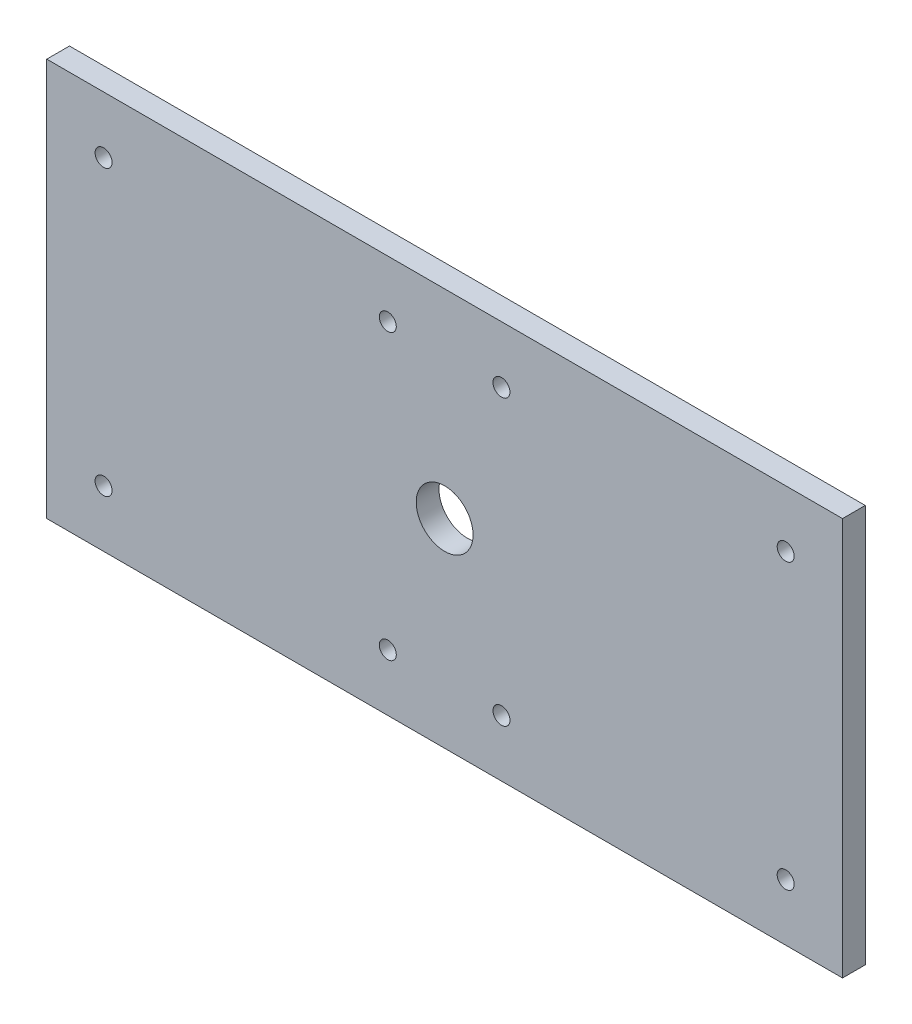
SolidWorks part; units mm, degrees
ref_plane "Front Plane" through (0, 0, 0) normal (0, 0, 1) x (1, 0, 0)
ref_plane "Top Plane" through (0, 0, 0) normal (0, 1, 0) x (1, 0, 0)
ref_plane "Right Plane" through (0, 0, 0) normal (1, 0, 0) x (0, 0, -1)
sketch "Sketch1" plane through (0, 0, 0) normal (0, 0, 1) x (1, 0, 0)
  line L1 (-88.9, 44.45) -> (88.9, 44.45)
  line L2 (-88.9, 44.45) -> (-88.9, -44.45)
  line L3 (-88.9, -44.45) -> (88.9, -44.45)
  line L4 (88.9, 44.45) -> (88.9, -44.45)
  line L5 (-88.9, 44.45) -> (88.9, -44.45) construction
  line L6 (-88.9, -44.45) -> (88.9, 44.45) construction
  circle A0 centre (0, 0) radius 6.35
  point P0 (0, 0)
  dimension "D3" = 12.7
  dimension "D1" = 88.9
  dimension "D2" = 177.8
extrude "Boss-Extrude1" add sketch "Sketch1" along normal blind 5.08
hole_wizard "#6 Clearance Hole1" positions "Sketch2" profile "Sketch4" hole size "#6" standard "ANSI Inch" end condition through all
sketch "Sketch2" plane through (0, 0, 5.08) normal (0, 0, 1) x (1, 0, 0)
  line L1 (-76.2, 31.75) -> (76.2, 31.75)
  line L2 (-76.2, 31.75) -> (-76.2, -31.75)
  line L3 (-76.2, -31.75) -> (76.2, -31.75)
  line L4 (76.2, 31.75) -> (76.2, -31.75)
  line L5 (-76.2, 31.75) -> (76.2, -31.75) construction
  line L6 (-76.2, -31.75) -> (76.2, 31.75) construction
  line L8 (-12.7, 31.75) -> (12.7, 31.75)
  line L9 (-12.7, 31.75) -> (-12.7, -31.75)
  line L10 (-12.7, -31.75) -> (12.7, -31.75)
  line L11 (12.7, 31.75) -> (12.7, -31.75)
  line L12 (-12.7, 31.75) -> (12.7, -31.75) construction
  line L13 (-12.7, -31.75) -> (12.7, 31.75) construction
  line L14 (-88.9, 44.45) -> (-88.9, -44.45) construction
  line L15 (88.9, 44.45) -> (-88.9, 44.45) construction
  point P2 (76.2, -31.75)
  point P29 (-76.2, 31.75)
  point P30 (-76.2, -31.75)
  point P31 (76.2, 31.75)
  point P34 (12.7, -31.75)
  point P63 (-12.7, 31.75)
  point P64 (-12.7, -31.75)
  point P65 (12.7, 31.75)
  point P71 (0, 0)
  dimension "D1" = 12.7
  dimension "D2" = 12.7
  dimension "D3" = 12.7
sketch "Sketch4" plane through (76.2, -31.75, 5.08) normal (1, 0, 0) x (0, -1, 0)
  line L0 (0, 0) -> (0, 5.08)
  line L1 (0, 5.08) -> (1.8986, 5.08)
  line L2 (1.8986, 5.08) -> (1.8986, 0)
  line L5 (1.8986, 0) -> (0, 0)
  line L11 (0, -6.35) -> (0, 107.95) construction
  dimension "Thru Hole Dia." = 3.7973
  dimension "Thru Hole Depth" = 5.08
